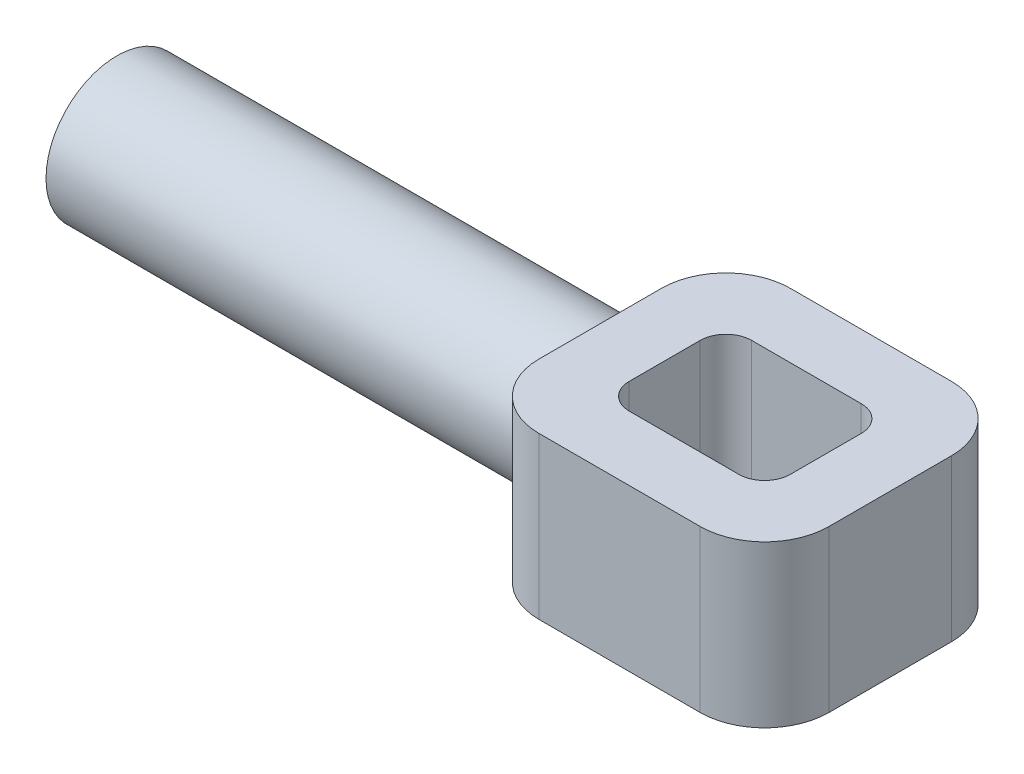
SolidWorks part; units mm, degrees
ref_plane "Front Plane" through (0, 0, 0) normal (0, 0, 1) x (1, 0, 0)
ref_plane "Top Plane" through (0, 0, 0) normal (0, 1, 0) x (1, 0, 0)
ref_plane "Right Plane" through (0, 0, 0) normal (1, 0, 0) x (0, 0, -1)
sketch "Sketch1" plane through (0, 0, 0) normal (0, 1, 0) x (1, 0, 0)
  line L1 (-12.5, 9.5) -> (12.5, 9.5)
  line L2 (-12.5, 9.5) -> (-12.5, -9.5)
  line L3 (-12.5, -9.5) -> (12.5, -9.5)
  line L4 (12.5, 9.5) -> (12.5, -9.5)
  line L5 (-12.5, 9.5) -> (12.5, -9.5) construction
  line L6 (-12.5, -9.5) -> (12.5, 9.5) construction
  point P0 (0, 0)
  dimension "D1" = 25
  dimension "D2" = 19
extrude "Extrude-Thin1" add sketch "Sketch1" along normal blind 25 thin thin type one direction wall 10
fillet "Fillet1" radius 10 4 edges at (22.5, 12.5, -19.5) (-22.5, 12.5, -19.5) (-22.5, 12.5, 19.5) (22.5, 12.5, 19.5)
fillet "Fillet2" radius 4 4 edges at (-12.5, 12.5, -9.5) (12.5, 12.5, -9.5) (-12.5, 12.5, 9.5) (12.5, 12.5, 9.5)
sketch "Sketch2" plane through (-22.5, 0, 3) normal (-1, 0, 0) x (0, 0, 1)
  line L0 (-3, 0) -> (-3, 25) construction
  line L2 (-12.5, 25) -> (6.5, 25) construction
  circle A1 centre (-3, 12.5) radius 11
  dimension "D2" = 22
extrude "Boss-Extrude1" add sketch "Sketch2" along normal blind 75
sketch "Sketch3" plane through (-97.5, 0, 0) normal (-1, 0, 0) x (0, 0, 1)
  circle A1 centre (0, 12.5) radius 7.85
  dimension "D2" = 15.7
extrude "Cut-Extrude1" cut sketch "Sketch3" against normal blind 30
